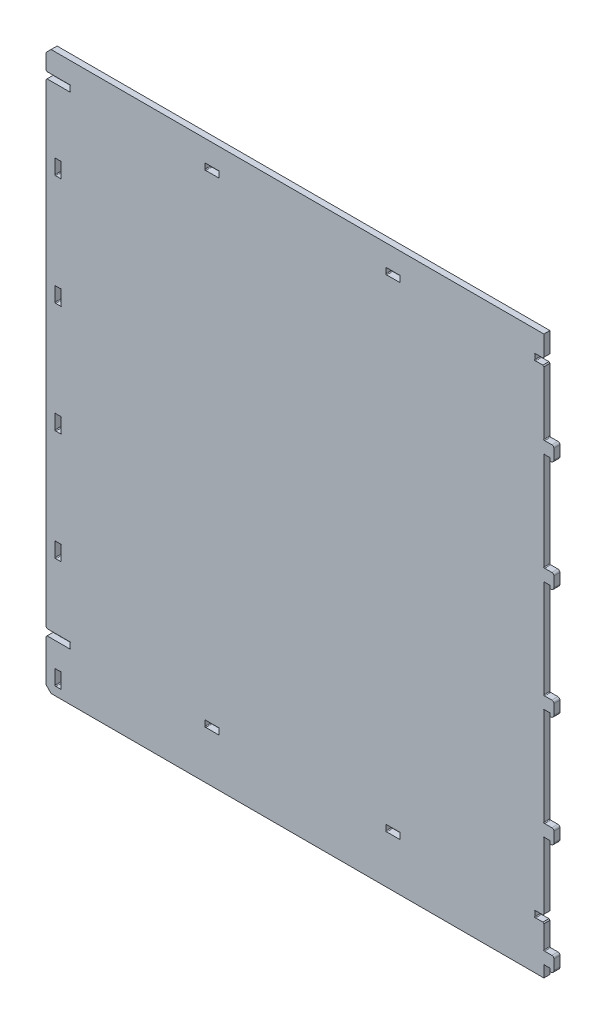
SolidWorks part; units mm, degrees
material "Acrylic (Medium-high impact)"
ref_plane "Front Plane" through (0, 0, 0) normal (0, 0, 1) x (1, 0, 0)
ref_plane "Top Plane" through (0, 0, 0) normal (0, 1, 0) x (1, 0, 0)
ref_plane "Right Plane" through (0, 0, 0) normal (1, 0, 0) x (0, 0, -1)
sketch "Sketch1" plane through (0, 0, 0) normal (0, 0, 1) x (1, 0, 0)
  line L0 (0, 555) -> (495.4, 555)
  line L1 (0, 555) -> (0, 0)
  line L2 (495.4, 555) -> (495.4, 0)
  line L3 (0, 0) -> (495.4, 0)
  dimension "D1" = 495.4
  dimension "D2" = 555
extrude "Boss-Extrude1" add sketch "Sketch1" along normal blind 6
sketch "Sketch3" plane through (0, 0, 6) normal (0, 0, 1) x (1, 0, 0)
  line L0 (495.4, 23.5) -> (503.4, 23.5)
  line L1 (495.4, 0) -> (495.4, 555) construction
  line L2 (501.4, 11.5) -> (505.4, 11.5) construction
  line L3 (501.4, 11.5) -> (495.4, 11.5)
  line L4 (495.4, 11.5) -> (495.4, 23.5)
  line L5 (0, 0) -> (495.4, 0) construction
  line L7 (505.4, 21.5) -> (505.4, 11.5)
  line L9 (501.4, 11.5) -> (501.4, 9.5)
  line L10 (502.4, 11.5) -> (502.4, 8.5) construction
  arc A0 (503.4, 23.5) -> (505.4, 21.5) centre (503.4, 21.5) cw
  arc A3 (501.4, 9.5) -> (502.4, 8.5) centre (502.4, 9.5) ccw
  arc A4 (502.4, 8.5) -> (505.4, 11.5) centre (502.4, 11.5) ccw
  dimension "D1" = 6
  dimension "D3" = 2
  dimension "D4" = 23.5
  dimension "D8" = 1
  dimension "D2" = 12
  dimension "D7" = 3
extrude "Boss-Extrude2" add sketch "Sketch3" against normal up to surface (6 mm away) up to face at (247.7, 277.5, 0)
sketch "Sketch2" plane through (0, 0, 6) normal (0, 0, 1) x (1, 0, 0)
  line L0 (9, 8.5) -> (9, 23.5)
  line L1 (0, 555) -> (0, 0) construction
  line L3 (15, 23.5) -> (15, 8.5)
  line L4 (15, 8.5) -> (9, 8.5)
  line L5 (9, 23.5) -> (15, 23.5)
  line L6 (15, 16) -> (0, 16) construction
  line L7 (495.4, 23.5) -> (15, 23.5) construction
  dimension "D2" = 6
  dimension "D3" = 15
  dimension "D4" = 15
extrude "Cut-Extrude1" cut sketch "Sketch2" against normal through all
sketch "Sketch6" plane through (0, 0, 6) normal (0, 0, 1) x (1, 0, 0)
  line L0 (9, 9.2071) -> (9, 8.5) construction
  line L1 (9, 23.5) -> (9, 8.5) construction
  line L2 (9, 8.5) -> (9.7071, 8.5) construction
  line L3 (9, 8.5) -> (15, 8.5) construction
  line L4 (9, 22.7929) -> (9, 23.5) construction
  line L5 (14.2929, 8.5) -> (15, 8.5) construction
  line L6 (15, 8.5) -> (15, 9.2071) construction
  line L7 (15, 8.5) -> (15, 23.5) construction
  line L8 (9, 23.5) -> (9.7071, 23.5) construction
  line L9 (15, 23.5) -> (9, 23.5) construction
  line L10 (495.4, 24.2071) -> (495.4, 23.5) construction
  line L11 (14.2929, 23.5) -> (15, 23.5) construction
  line L12 (15, 23.5) -> (15, 22.7929) construction
  line L13 (495.4, 23.5) -> (495.4, 555) construction
  line L14 (495.4, 23.5) -> (496.1071, 23.5) construction
  line L15 (503.4, 23.5) -> (495.4, 23.5) construction
  line L16 (495.4, 11.5) -> (501.4, 11.5) construction
  line L17 (500.6929, 11.5) -> (501.4, 11.5) construction
  line L19 (495.4, 11.5) -> (501.4, 11.5) construction
  line L20 (501.4, 11.5) -> (501.4, 10.7929) construction
  line L21 (496.1071, 11.5) -> (495.4, 11.5) construction
  line L22 (495.4, 11.5) -> (495.4, 10.7929) construction
  line L23 (495.4, 0) -> (495.4, 11.5) construction
  line L24 (501.4, 11.5) -> (501.4, 9.5) construction
  circle A0 centre (9.3536, 8.8536) radius 0.5
  circle A1 centre (14.6464, 8.8536) radius 0.5
  circle A2 centre (14.6464, 23.1464) radius 0.5
  circle A3 centre (9.3536, 23.1464) radius 0.5
  circle A4 centre (495.7536, 23.8536) radius 0.5
  circle A5 centre (501.0464, 11.1464) radius 0.5
  circle A6 centre (495.7536, 11.1464) radius 0.5
  dimension "D1" = 1
extrude "Cut-Extrude4" cut sketch "Sketch6" against normal through all
pattern_linear "LPattern1" count 5 spacing 110 along (0, 1, 0) of "Boss-Extrude2", "Cut-Extrude1", "Cut-Extrude4"
sketch "Sketch5" plane through (0, 0, 6) normal (0, 0, 1) x (1, 0, 0)
  line L0 (0, 555) -> (0, 0) construction
  line L1 (0, 47.7) -> (24, 47.7)
  line L2 (0, 47.7) -> (0, 53.9)
  line L3 (0, 53.9) -> (24, 53.9)
  line L4 (24, 47.7) -> (24, 53.9)
  line L5 (0, 0) -> (495.4, 0) construction
  line L6 (495.4, 23.5) -> (495.4, 121.5) construction
  line L7 (486.4, 47.7) -> (495.4, 47.7)
  line L8 (486.4, 47.7) -> (486.4, 53.9)
  line L9 (486.4, 53.9) -> (495.4, 53.9)
  line L10 (495.4, 47.7) -> (495.4, 53.9)
  dimension "D1" = 6.2
  dimension "D2" = 24
  dimension "D3" = 9
  dimension "D4" = 47.7
extrude "Cut-Extrude3" cut sketch "Sketch5" against normal up to next (6 mm away)
sketch "Sketch7" plane through (0, 0, 6) normal (0, 0, 1) x (1, 0, 0)
  line L0 (23.2929, 47.7) -> (24, 47.7) construction
  line L1 (0, 47.7) -> (24, 47.7) construction
  line L2 (24, 47.7) -> (24, 48.4071) construction
  line L3 (24, 47.7) -> (24, 53.9) construction
  line L4 (486.4, 53.1929) -> (486.4, 53.9) construction
  line L5 (24, 53.1929) -> (24, 53.9) construction
  line L6 (24, 53.9) -> (23.2929, 53.9) construction
  line L7 (24, 53.9) -> (0, 53.9) construction
  line L8 (486.4, 53.9) -> (486.4, 47.7) construction
  line L9 (486.4, 53.9) -> (487.1071, 53.9) construction
  line L10 (495.4, 53.9) -> (486.4, 53.9) construction
  line L11 (486.4, 47.7) -> (495.4, 47.7) construction
  line L12 (486.4, 48.4071) -> (486.4, 47.7) construction
  line L13 (486.4, 47.7) -> (487.1071, 47.7) construction
  circle A0 centre (486.7536, 53.5464) radius 0.5
  circle A1 centre (486.7536, 48.0536) radius 0.5
  circle A2 centre (23.6464, 53.5464) radius 0.5
  circle A3 centre (23.6464, 48.0536) radius 0.5
  dimension "D1" = 1
extrude "Cut-Extrude5" cut sketch "Sketch7" against normal through all
sketch "Sketch8" plane through (0, 0, 6) normal (0, 0, 1) x (1, 0, 0)
  line L1 (158.2, 53.9) -> (172.2, 53.9)
  line L2 (158.2, 53.9) -> (158.2, 47.7)
  line L3 (158.2, 47.7) -> (172.2, 47.7)
  line L4 (172.2, 53.9) -> (172.2, 47.7)
  line L5 (0, 47.7) -> (24, 47.7) construction
  line L6 (0, 53.9) -> (24, 53.9) construction
  line L7 (165.2, 53.9) -> (165.2, 47.7) construction
  line L8 (165.2, 50.8) -> (345.2, 50.8) construction
  line L9 (255.2, 50.8) -> (255.2, 7.924) construction
  line L10 (15, 7.924) -> (495.4, 7.924) construction
  line L11 (15, 9.2071) -> (15, 22.7929) construction
  line L12 (495.4, 0) -> (495.4, 10.7929) construction
  dimension "D1" = 14
  dimension "D2" = 180
extrude "Cut-Extrude6" cut sketch "Sketch8" against normal through all
sketch "Sketch9" plane through (0, 0, 6) normal (0, 0, 1) x (1, 0, 0)
  line L0 (171.4929, 53.9) -> (172.2, 53.9) construction
  line L1 (158.2, 53.9) -> (158.9071, 53.9) construction
  line L2 (158.2, 53.9) -> (158.2, 53.1929) construction
  line L3 (158.2, 47.7) -> (158.9071, 47.7) construction
  line L4 (172.2, 53.9) -> (172.2, 53.1929) construction
  line L5 (158.2, 48.4071) -> (158.2, 47.7) construction
  line L6 (171.4929, 47.7) -> (172.2, 47.7) construction
  line L7 (172.2, 48.4071) -> (172.2, 47.7) construction
  circle A0 centre (158.5536, 53.5464) radius 0.5
  circle A1 centre (158.5536, 48.0536) radius 0.5
  circle A2 centre (171.8464, 48.0536) radius 0.5
  circle A3 centre (171.8464, 53.5464) radius 0.5
  dimension "D1" = 1
extrude "Cut-Extrude7" cut sketch "Sketch9" against normal through all
pattern_linear "LPattern4" count 2 spacing 180 along (1, 0, 0) of "Cut-Extrude6", "Cut-Extrude7"
chamfer "Chamfer2" distance 1 angle 45 4 edges at (0, 53.9, 3) (0, 47.7, 3) (495.4, 53.9, 3) (495.4, 47.7, 3)
pattern_linear "LPattern3" count 2 spacing 480 along (0, 1, 0) of "Chamfer2", "Cut-Extrude3", "Cut-Extrude5", "LPattern4", "Cut-Extrude6", "Cut-Extrude7"
chamfer "Chamfer1" distance 5 angle 45 2 edges at (0, 0, 3) (0, 555, 3)
other "Save Bodies1"
